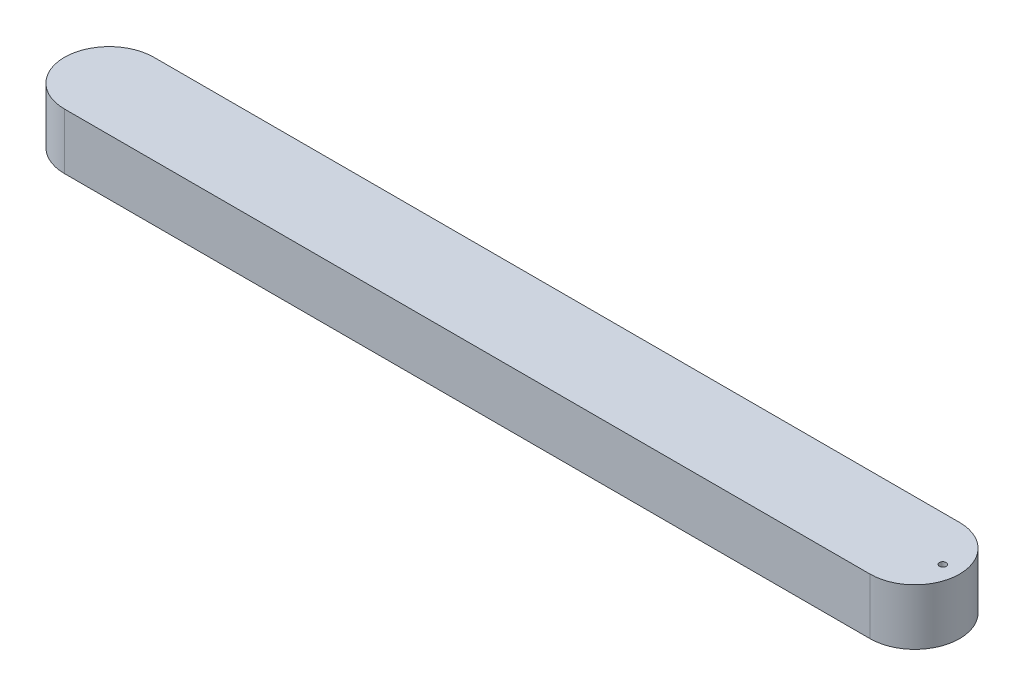
SolidWorks part; units mm, degrees
material "Teak"
ref_plane "Front Plane" through (0, 0, 0) normal (0, 0, 1) x (1, 0, 0)
ref_plane "Top Plane" through (0, 0, 0) normal (0, 1, 0) x (1, 0, 0)
ref_plane "Right Plane" through (0, 0, 0) normal (1, 0, 0) x (0, 0, -1)
sketch "Sketch1" plane through (0, 0, 0) normal (0, 1, 0) x (1, 0, 0)
  line L1 (-360, 40) -> (360, 40)
  line L3 (-360, -40) -> (360, -40)
  arc A0 (360, 40) -> (360, -40) centre (360, 0) cw
  arc A1 (-360, -40) -> (-360, 40) centre (-360, 0) cw
  point P0 (0, 0)
  dimension "D4" = 40
  dimension "D3" = 40
  dimension "D1" = 360
  dimension "D2" = 40
  dimension "D5" = 80
  dimension "D6" = 360
  dimension "D7" = 360
  dimension "D8" = 360
extrude "Boss-Extrude1" add sketch "Sketch1" along normal blind 50
sketch "Sketch4" plane through (0, 0, 0) normal (0, -1, 0) x (1, 0, 0)
  line L8 (360, 35) -> (-360, 35)
  line L9 (-360, -35) -> (360, -35)
  line L10 (360, 35) -> (-360, 35)
  line L11 (-360, -35) -> (360, -35)
  arc A6 (-360, 35) -> (-360, -35) centre (-360, 0) ccw
  arc A7 (360, -35) -> (360, 35) centre (360, 0) ccw
  arc A8 (-360, 35) -> (-360, -35) centre (-360, 0) ccw
  arc A9 (360, -35) -> (360, 35) centre (360, 0) ccw
  dimension "D1" = 5
extrude "Cut-Extrude2" cut sketch "Sketch4" against normal blind 4
sketch "Sketch15" plane through (0, 4, 0) normal (0, -1, 0) x (1, 0, 0)
  line L1 (360, -30) -> (-360, -30)
  line L2 (360, -22) -> (360, 22)
  line L3 (360, 30) -> (-360, 30)
  line L4 (-360, -22) -> (-360, 22)
  line L6 (-360, 40) -> (360, 40) construction
  arc A0 (360, -30) -> (360, -22) centre (360, -26) ccw
  arc A1 (360, 22) -> (360, 30) centre (360, 26) ccw
  arc A2 (360, 22) -> (360, 30) centre (360, 26) ccw
  arc A3 (-360, -30) -> (-360, -22) centre (-360, -26) cw
  arc A4 (-360, 30) -> (-360, 22) centre (-360, 26) ccw
  point P0 (0, 0)
  point P8 (0, 0)
  dimension "D3" = 4
  dimension "D4" = 4
  dimension "D6" = 4
  dimension "D9" = 4
  dimension "D2" = 60
  dimension "D5" = 360
  dimension "D7" = 4
  dimension "D8" = 360
  dimension "D11" = 360
  dimension "D13" = 10
  dimension "D14" = 360
extrude "Cut-Extrude14" cut sketch "Sketch15" against normal blind 6
sketch "Sketch2" plane through (0, 4, 0) normal (0, -1, 0) x (1, 0, 0)
  line L0 (360, -40) -> (-360, -40) construction
  line L1 (356, -27) -> (-356, -27)
  line L2 (360, -23) -> (360, 23)
  line L3 (356, 27) -> (-356, 27)
  line L4 (-360, -23) -> (-360, 23)
  line L5 (-360, 40) -> (360, 40) construction
  arc A0 (356, -27) -> (360, -23) centre (356, -23) ccw
  arc A1 (360, 23) -> (356, 27) centre (356, 23) ccw
  arc A2 (-360, -23) -> (-356, -27) centre (-356, -23) ccw
  arc A3 (-356, 27) -> (-360, 23) centre (-356, 23) ccw
  point P1 (0, 0)
  dimension "D3" = 4
  dimension "D4" = 720
  dimension "D1" = 8
  dimension "D7" = 4
  dimension "D9" = 8
  dimension "D11" = 8
  dimension "D12" = 4
  dimension "D14" = 4
  dimension "D15" = 4
  dimension "D16" = 8
  dimension "D5" = 13
  dimension "D6" = 13
  dimension "D8" = 4
  dimension "D13" = 4
  dimension "D17" = 360
extrude "Cut-Extrude16" cut sketch "Sketch2" against normal blind 30
hole_wizard "Hole1" positions "Sketch17" profile "Sketch16" legacy end condition through all
sketch "Sketch17" plane through (0, 4, 0) normal (0, -1, 0) x (-1, 0, 0)
  line L1 (360, -40) -> (-360, -40) construction
  line L3 (-360, 22) -> (-360, -22) construction
  point P0 (-385, 0)
  dimension "D1" = 25
  dimension "D2" = 40
sketch "Sketch16" plane through (385, 4, 0) normal (1, 0, 0) x (0, 0, -1)
  line L0 (0, 0) -> (0, 46)
  line L1 (0, 46) -> (3, 46)
  line L2 (3, 46) -> (3, 0)
  line L5 (3, 0) -> (0, 0)
  line L11 (0, -6.35) -> (0, 107.95) construction
  dimension "Thru Hole Dia." = 6
  dimension "Thru Hole Depth" = 46
